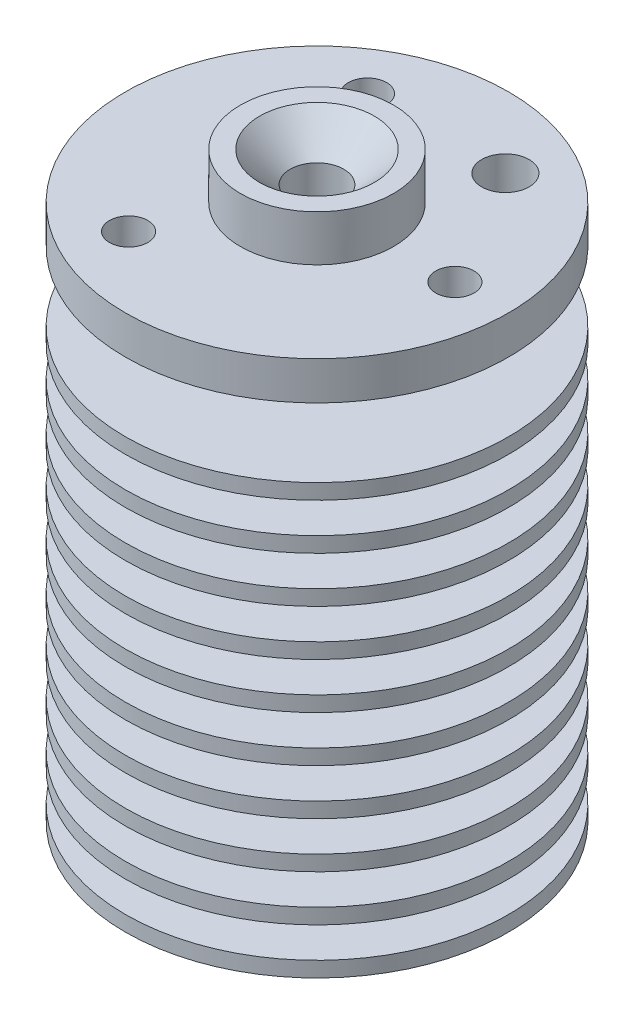
SolidWorks part; units mm, degrees
ref_plane "Front Plane" through (0, 0, 0) normal (0, 0, 1) x (1, 0, 0)
ref_plane "Top Plane" through (0, 0, 0) normal (0, 1, 0) x (1, 0, 0)
ref_plane "Right Plane" through (0, 0, 0) normal (1, 0, 0) x (0, 0, -1)
sketch "Sketch1" plane through (0, 0, 0) normal (0, 0, 1) x (1, 0, 0)
  line L0 (-2.5, 0) -> (-2.5, 8)
  line L1 (-2.5, 8) -> (-0.8, 8)
  line L2 (-0.8, 8) -> (-0.8, 36)
  line L3 (-0.8, 36) -> (-12.5, 36)
  line L4 (-12.5, 36) -> (-12.5, 0)
  line L5 (-12.5, 0) -> (-2.5, 0)
  line L6 (0, 0) -> (0, 131.8203) construction
  line L7 (0, 0) -> (-2.5, 0) construction
  dimension "D1" = 5
  dimension "D2" = 12.5
  dimension "D3" = 8
  dimension "D4" = 36
  dimension "D5" = 1.6
revolve "Revolve1" add sketch "Sketch1" angle 360 about L6
cosmetic thread "Rosca cosmética1" parameters "D1"=5, "D2"=6
ref_axis "Axis1" through (0, 36, 0) along (0, -1, 0)
sketch "Sketch2" plane through (0, 0, 0) normal (1, 0, 0) x (0, 0, -1)
  line L0 (12.5, 34) -> (3.5, 34)
  line L1 (12.5, 0) -> (12.5, 36) construction
  line L2 (3.5, 34) -> (3.5, 32)
  line L3 (3.5, 32) -> (12.5, 32)
  line L4 (12.5, 0) -> (12.5, 36) construction
  line L5 (12.5, 32) -> (12.5, 34)
  line L6 (12.5, 36) -> (-12.5, 36) construction
  dimension "D1" = 9
  dimension "D2" = 2
  dimension "D3" = 2
revolve "Cut-Revolve1" cut sketch "Sketch2" angle 360 about axis through (0, 36, 0) along (0, -1, 0)
pattern_linear "LPattern1" count 11 spacing 3 along (0, -1, 0) of "Cut-Revolve1"
sketch "Sketch3" plane through (0, 36, 0) normal (0, 1, 0) x (1, 0, 0)
  circle A0 centre (0, 0) radius 5
  dimension "D1" = 10
extrude "Boss-Extrude1" add sketch "Sketch3" along normal blind 3
sketch "Sketch4" plane through (0, 39, 0) normal (0, 1, 0) x (1, 0, 0)
  circle A0 centre (0, 0) radius 1.75
  dimension "D1" = 3.5
extrude "Cut-Extrude1" cut sketch "Sketch4" against normal through all
chamfer "Chamfer1" distance 2 angle 45 1 edges at (0, 39, 1.75)
sketch "Sketch5" plane through (0, 36, 0) normal (0, 1, 0) x (1, 0, 0)
  circle A0 centre (0, 0) radius 9 construction
  circle A1 centre (9, 0) radius 1.25
  circle A2 centre (-4.5, -7.7942) radius 1.25
  circle A3 centre (-4.5, 7.7942) radius 1.25
  point P11 (0, 0)
  dimension "D1" = 18
  dimension "D2" = 2.5
  dimension "D3" = 3
extrude "Cut-Extrude2" cut sketch "Sketch5" against normal blind 2
cosmetic thread "Rosca cosmética2" parameters "D2"=3
cosmetic thread "Rosca cosmética3" parameters "D2"=3
cosmetic thread "Rosca cosmética4" parameters "D2"=3
sketch "Sketch6" plane through (0, 0, 0) normal (0, -1, 0) x (1, 0, 0)
  circle A1 centre (0, 0) radius 12.5
  circle A2 centre (0, 0) radius 12.5
  dimension "D1" = 0
extrude "Cut-Extrude3" cut sketch "Sketch6" against normal blind 1
sketch "Sketch7" plane through (0, 32, 0) normal (0, 1, 0) x (1, 0, 0)
  circle A0 centre (0, 0) radius 3.5 construction
  circle A1 centre (0, 0) radius 12.5
  circle A2 centre (0, 0) radius 12.5
  circle A3 centre (0, 0) radius 3.5
  dimension "D1" = 0
extrude "Cut-Extrude5" cut sketch "Sketch7" against normal up to next
sketch "Sketch8" plane through (0, 2, 0) normal (0, 1, 0) x (1, 0, 0)
  circle A0 centre (0, 0) radius 3.5 construction
  circle A1 centre (0, 0) radius 3.5
  circle A2 centre (0, 0) radius 5
  dimension "D1" = 1.5
extrude "Boss-Extrude2" add sketch "Sketch8" along normal up to surface (8 mm away) up to face at (0, 10, 3.5)
sketch "Sketch9" plane through (0, 34, 0) normal (0, -1, 0) x (1, 0, 0)
  circle A0 centre (9, 0) radius 1.25 construction
  circle A1 centre (0, 0) radius 12.5
  circle A2 centre (0, 0) radius 12.5
  circle A3 centre (0, 0) radius 3.5 construction
  circle A4 centre (-4.5, 7.7942) radius 1.25 construction
  circle A5 centre (-4.5, -7.7942) radius 1.25 construction
  circle A6 centre (9, 0) radius 1.25
  circle A7 centre (0, 0) radius 3.5
  circle A8 centre (-4.5, 7.7942) radius 1.25
  circle A9 centre (-4.5, -7.7942) radius 1.25
  dimension "D1" = 0
extrude "Boss-Extrude3" add sketch "Sketch9" along normal blind 0.5
sketch "Croquis1" plane through (0, 36, 0) normal (0, 1, 0) x (1, 0, 0)
  line L0 (0, 0) -> (12.5, 0) construction
  line L1 (0, 0) -> (4.5, 7.7942) construction
  circle A0 centre (4.5, 7.7942) radius 1.55
  circle A1 centre (0, 0) radius 12.5 construction
  dimension "D1" = 3.1
  dimension "D2" = 60
  dimension "D3" = 9
extrude "Cortar-Extruir1" cut sketch "Croquis1" against normal up to surface (2.5 mm away) up to face at (-4.5, 33.5, 6.5442)
